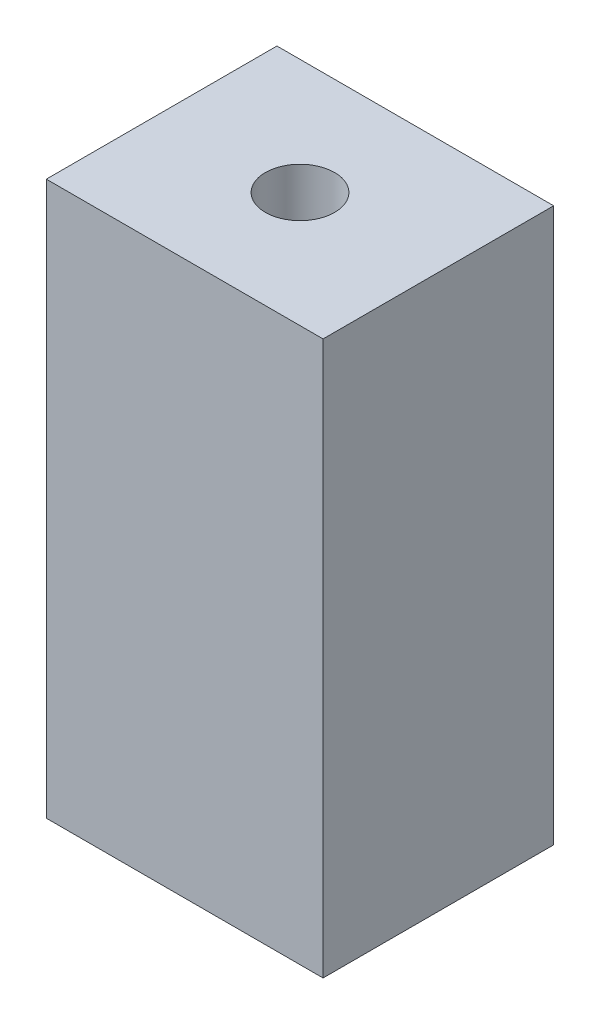
SolidWorks part; units mm, degrees
ref_plane "Front Plane" through (0, 0, 0) normal (0, 0, 1) x (1, 0, 0)
ref_plane "Top Plane" through (0, 0, 0) normal (0, 1, 0) x (1, 0, 0)
ref_plane "Right Plane" through (0, 0, 0) normal (1, 0, 0) x (0, 0, -1)
sketch "Sketch1" plane through (0, 0, 0) normal (0, 1, 0) x (1, 0, 0)
  line L1 (-6, -5) -> (6, -5)
  line L2 (-6, -5) -> (-6, 5)
  line L3 (-6, 5) -> (6, 5)
  line L4 (6, -5) -> (6, 5)
  line L5 (-6, -5) -> (6, 5) construction
  line L6 (-6, 5) -> (6, -5) construction
  circle A0 centre (0, 0) radius 1.5
  point P0 (0, 0)
  dimension "D3" = 3
  dimension "D1" = 10
  dimension "D2" = 12
extrude "Boss-Extrude1" add sketch "Sketch1" along normal blind 24
sketch "Sketch2" plane through (0, 0, 0) normal (0, -1, 0) x (1, 0, 0)
  circle A0 centre (0, 0) radius 1.5
  circle A1 centre (0, 0) radius 1.754
  dimension "D1" = 0.254
extrude "Boss-Extrude2" add sketch "Sketch2" along normal blind 0.5
hole_wizard "Tap Drill for M1.6x0.35 Tap1" positions "Sketch3" profile "Sketch4" hole size "M1.6x0.35" standard "ANSI Metric"
sketch "Sketch3" plane through (0, 0, 0) normal (0, -1, 0) x (-1, 0, 0)
  line L0 (6, 0) -> (-6, 0) construction
  line L1 (6, 5) -> (6, -5) construction
  line L2 (-6, -5) -> (-6, 5) construction
  point P8 (4.5, 0)
  point P10 (-4.5, 0)
  dimension "D1" = 4.5
  dimension "D2" = 4.5
sketch "Sketch4" plane through (4.5, 0, 0) normal (1, 0, 0) x (0, 0, -1)
  line L0 (0, 0) -> (0, 1)
  line L1 (0, 1) -> (0.625, 0.6245)
  line L2 (0.625, 0.6245) -> (0.625, 0)
  line L5 (0.625, 0) -> (0, 0)
  line L10 (0, 1) -> (-0.625, 0.6245) construction
  line L11 (0, -6.35) -> (0, 107.95) construction
  dimension "Hole Dia." = 1.25
  dimension "Hole Depth" = 1
  dimension "Drill Angle" = 118
